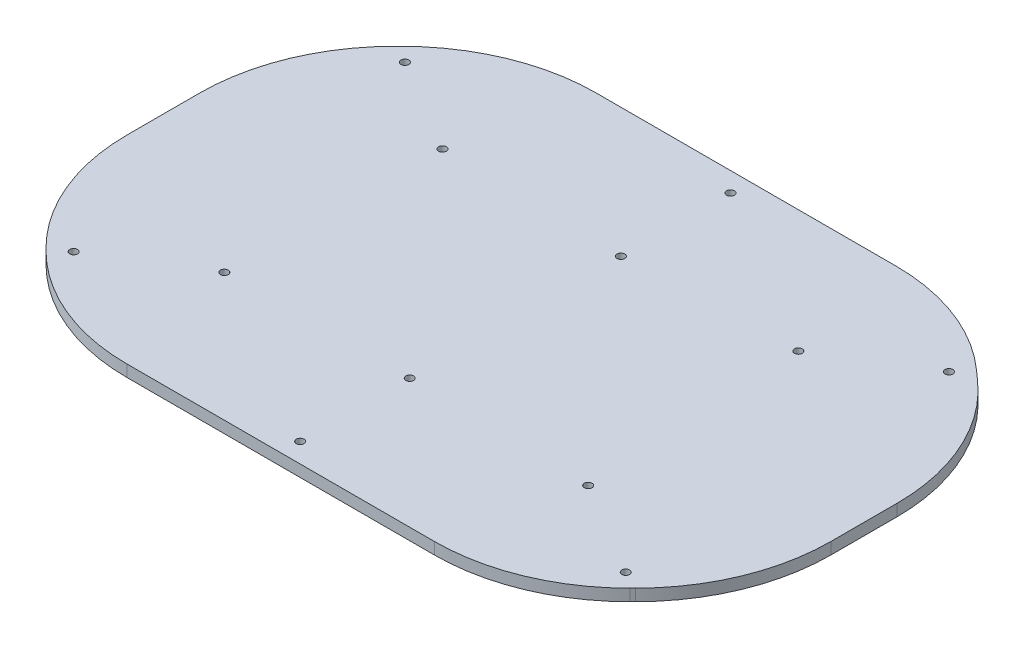
SolidWorks part; units mm, degrees
ref_plane "Front Plane" through (0, 0, 0) normal (0, 0, 1) x (1, 0, 0)
ref_plane "Top Plane" through (0, 0, 0) normal (0, 1, 0) x (1, 0, 0)
ref_plane "Right Plane" through (0, 0, 0) normal (1, 0, 0) x (0, 0, -1)
sketch "Sketch1" plane through (0, 0, 0) normal (0, 1, 0) x (1, 0, 0)
  line L0 (27.0345, -59.3831) -> (27.0345, -77.9618)
  line L3 (77.7452, -128.6725) -> (156.3238, -128.6725)
  line L5 (41.6792, -24.0278) -> (42.3898, -23.3171)
  line L6 (77.7452, -8.6725) -> (154.3548, -8.6725)
  line L7 (187.6494, -21.3701) -> (190.3291, -23.7619)
  line L8 (207.0345, -61.0643) -> (207.0345, -77.9618)
  line L9 (192.3898, -113.3171) -> (191.6792, -114.0278)
  line L10 (165.5934, -128.6725) -> (32.5519, -128.6725)
  line L11 (42.3898, -114.0278) -> (41.6792, -113.3171)
  line L17 (70.3654, -8.6725) -> (125.3807, -8.6725)
  arc A0 (42.3898, -23.3171) -> (77.7452, -8.6725) centre (77.7452, -58.6725) cw
  arc A1 (154.3548, -8.6725) -> (187.6494, -21.3701) centre (154.3548, -58.6725) cw
  arc A2 (190.3291, -23.7619) -> (207.0345, -61.0643) centre (157.0345, -61.0643) cw
  arc A3 (192.3898, -113.3171) -> (207.0345, -77.9618) centre (157.0345, -77.9618) ccw
  arc A4 (156.3238, -128.6725) -> (191.6792, -114.0278) centre (156.3238, -78.6725) ccw
  arc A5 (77.7452, -128.6725) -> (42.3898, -114.0278) centre (77.7452, -78.6725) cw
  arc A6 (41.6792, -113.3171) -> (27.0345, -77.9618) centre (77.0345, -77.9618) cw
  arc A7 (27.0345, -59.3831) -> (41.6792, -24.0278) centre (77.0345, -59.3831) cw
  point P4 (57.0345, -8.6725)
  point P15 (173.4233, -8.6725)
  point P18 (207.0345, -38.6725)
  point P21 (207.0345, -98.6725)
  point P28 (27.0345, -98.6725)
  point P31 (27.0345, -38.6725)
  point P32 (0, 0)
  point P33 (0, 0)
  dimension "D10" = 50
  dimension "D11" = 50
  dimension "D1" = 60
  dimension "D2" = 60
  dimension "D3" = 45
  dimension "D4" = 120
  dimension "D5" = 30
  dimension "D6" = 45
  dimension "D7" = 180
  dimension "D8" = 30
extrude "Boss-Extrude1" add sketch "Sketch1" along normal blind 3 contours L11 L3 L9 L8 L7 L6 L5 L0
sketch "Sketch3" plane through (0, 3, 0) normal (0, 1, 0) x (1, 0, 0)
  line L0 (41.6792, -24.0278) -> (42.3898, -23.3171) construction
  line L1 (42.3898, -114.0278) -> (41.6792, -113.3171) construction
  line L6 (77.7452, -128.6725) -> (156.3238, -128.6725) construction
  line L7 (117.0345, -128.6725) -> (117.0345, -8.6725) construction
  line L8 (77.7452, -8.6725) -> (154.3548, -8.6725) construction
  line L11 (187.6494, -21.3701) -> (190.3291, -23.7619) construction
  line L14 (192.3898, -113.3171) -> (191.6792, -114.0278) construction
  line L18 (27.0345, -68.6725) -> (207.0345, -68.6725) construction
  line L19 (27.0345, -59.3831) -> (27.0345, -77.9618) construction
  line L20 (207.0345, -61.0643) -> (207.0345, -77.9618) construction
  line L23 (188.9893, -22.566) -> (41.6792, -113.3171) construction
  line L25 (42.0345, -23.6725) -> (192.0345, -113.6725) construction
  circle A0 centre (70.4637, -40.73) radius 1
  circle A1 centre (46.4539, -26.3241) radius 1
  circle A2 centre (117.0345, -41.6725) radius 1
  circle A3 centre (184.5468, -25.3028) radius 1
  circle A4 centre (117.0345, -13.6725) radius 1
  circle A5 centre (160.7075, -39.9891) radius 1
  circle A6 centre (163.6053, -96.6149) radius 1
  circle A7 centre (187.6151, -111.0208) radius 1
  circle A8 centre (117.0345, -95.6725) radius 1
  circle A9 centre (117.0345, -123.6725) radius 1
  circle A10 centre (46.0547, -110.6216) radius 1
  circle A11 centre (69.894, -95.9353) radius 1
  dimension "D19" = 0
  dimension "D20" = 0
  dimension "D21" = 5
  dimension "D22" = 2
  dimension "D23" = 0
  dimension "D24" = 0
  dimension "D25" = 0
  dimension "D26" = 0
  dimension "D3" = 28
  dimension "D4" = 28
  dimension "D7" = 28
  dimension "D8" = 28
  dimension "D9" = 5
  dimension "D10" = 0
  dimension "D11" = 5
  dimension "D12" = 0
  dimension "D13" = 0
  dimension "D14" = 0
  dimension "D15" = 0
  dimension "D18" = 5
  dimension "D1" = 5
  dimension "D5" = 28
  dimension "D6" = 28
  dimension "D16" = 5
  dimension "D17" = 0
extrude "Cut-Extrude1" cut sketch "Sketch3" against normal through all
